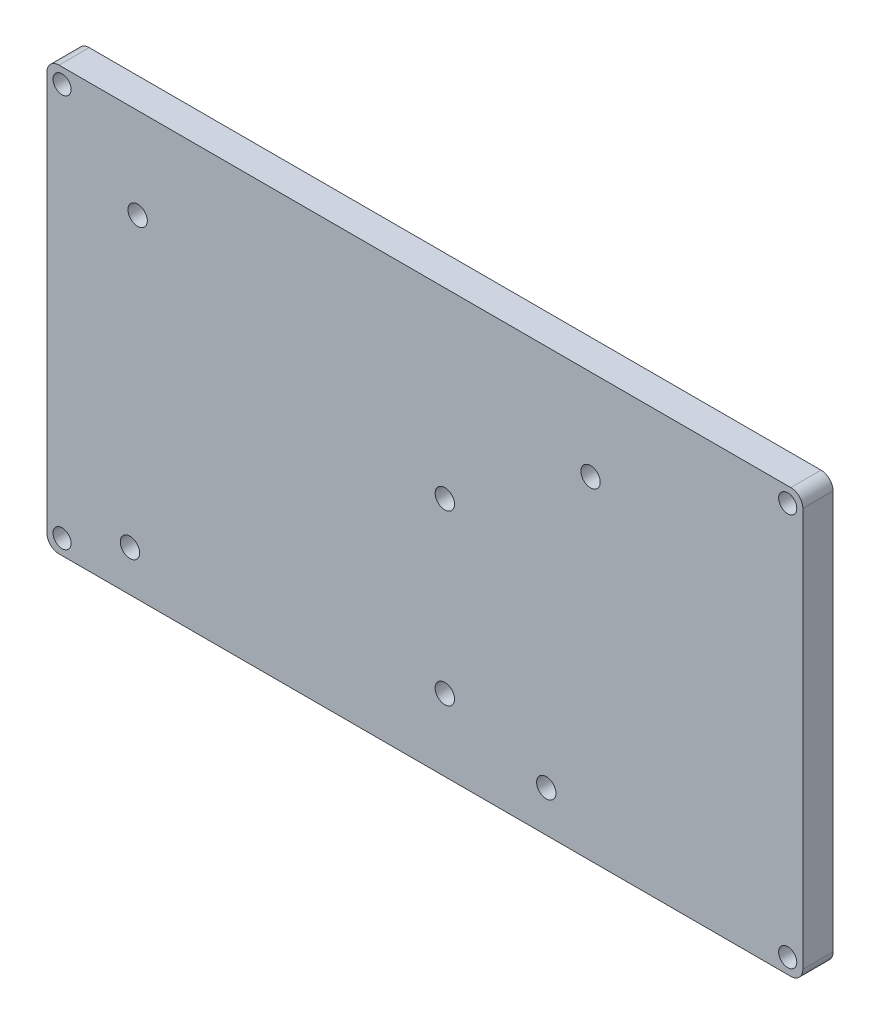
SolidWorks part; units mm, degrees
ref_plane "Front Plane" through (0, 0, 0) normal (0, 0, 1) x (1, 0, 0)
ref_plane "Top Plane" through (0, 0, 0) normal (0, 1, 0) x (1, 0, 0)
ref_plane "Right Plane" through (0, 0, 0) normal (1, 0, 0) x (0, 0, -1)
sketch "Sketch1" plane through (0, 0, 0) normal (0, 0, 1) x (1, 0, 0)
  line L0 (62.5, 35) -> (70.1002, 35) construction
  line L1 (0, 0) -> (125, 0)
  line L2 (0, 0) -> (0, 70)
  line L3 (0, 70) -> (125, 70)
  line L4 (125, 0) -> (125, 70)
  line L5 (62.5, 35) -> (62.5, 43.1493) construction
  circle A0 centre (15, 55) radius 1.6
  circle A1 centre (13.73, 6.8) radius 1.6
  circle A2 centre (82.5735, 6.8) radius 1.6
  circle A3 centre (89.9, 55) radius 1.6
  circle A4 centre (65.8, 39.8) radius 1.6
  circle A5 centre (65.8, 11.9) radius 1.6
  circle A6 centre (2.5, 67.5) radius 1.5
  circle A7 centre (122.5, 67.5) radius 1.5
  circle A8 centre (122.5, 2.5) radius 1.5
  circle A9 centre (2.5, 2.5) radius 1.5
  dimension "D6" = 3.2
  dimension "D7" = 3.2
  dimension "D8" = 3.2
  dimension "D9" = 3.2
  dimension "3.2" = 3.2
  dimension "D10" = 3.2
  dimension "D19" = 3
  dimension "D1" = 24.1
  dimension "D2" = 50.8
  dimension "D3" = 15.2
  dimension "D4" = 27.9
  dimension "D5" = 5.1
  dimension "D11" = 0
  dimension "D12" = 0
  dimension "D13" = 52.07
  dimension "D14" = 48.2
  dimension "D15" = 125
  dimension "D16" = 70
  dimension "D17" = 15
  dimension "D18" = 15
  dimension "D20" = 2.5
  dimension "D21" = 2.5
  dimension "D22" = 2
extrude "Boss-Extrude1" add sketch "Sketch1" along normal blind 5
fillet "Fillet1" radius 2 4 edges at (0, 0, 2.5) (0, 70, 2.5) (125, 70, 2.5) (125, 0, 2.5)
